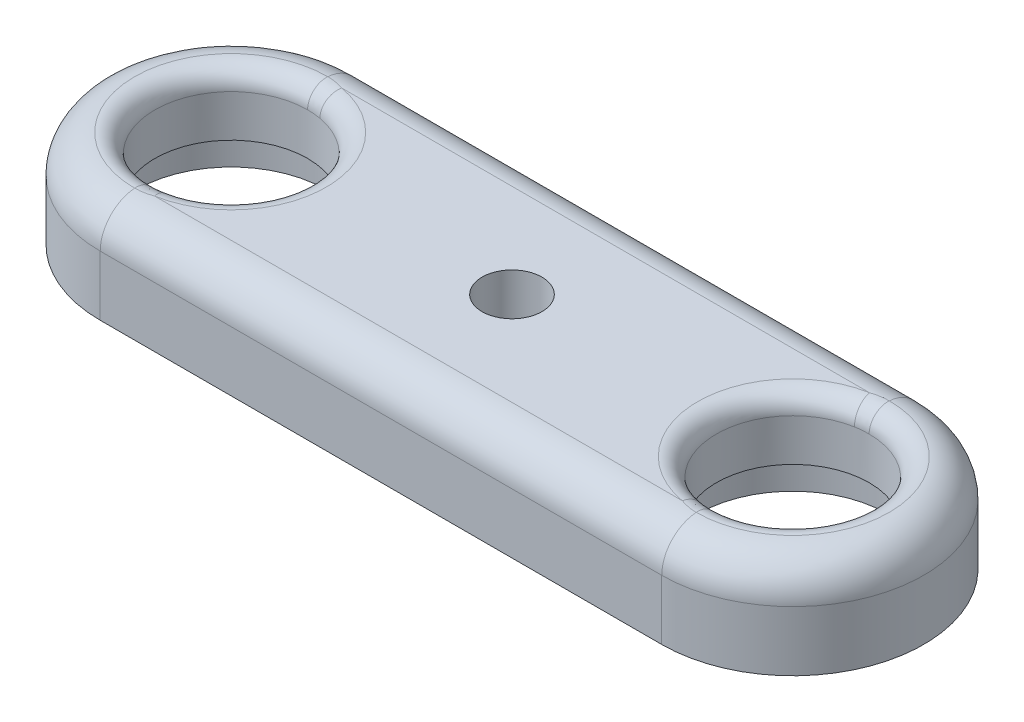
SolidWorks part; units mm, degrees
material "6061 Alloy"
ref_plane "Front Plane" through (0, 0, 0) normal (0, 0, 1) x (1, 0, 0)
ref_plane "Top Plane" through (0, 0, 0) normal (0, 1, 0) x (1, 0, 0)
ref_plane "Right Plane" through (0, 0, 0) normal (1, 0, 0) x (0, 0, -1)
sketch "Sketch1" plane through (0, 0, 0) normal (0, 1, 0) x (1, 0, 0)
  line L0 (-15, 0) -> (15, 0) construction
  line L1 (-15, 7) -> (15, 7)
  line L2 (-15, -7) -> (15, -7)
  arc A0 (-15, 7) -> (-15, -7) centre (-15, 0) ccw
  arc A1 (15, -7) -> (15, 7) centre (15, 0) ccw
  circle A2 centre (-15, 0) radius 4.08
  circle A3 centre (15, 0) radius 4.08
  point P3 (0, 0)
  dimension "D2" = 8.16
  dimension "D3" = 8.16
  dimension "D4" = 7
  dimension "D5" = 15
  dimension "D1" = 30
extrude "Boss-Extrude1" add sketch "Sketch1" along normal blind 5.2
sketch "Sketch2" plane through (0, 5.2, 0) normal (0, 1, 0) x (1, 0, 0)
  circle A3 centre (0, 0) radius 1.6
  dimension "D1" = 3.2
extrude "Cut-Extrude1" cut sketch "Sketch2" against normal blind 5.2
sketch "Sketch3" plane through (0, 0, 0) normal (0, -1, 0) x (1, 0, 0)
  circle A0 centre (-15, 0) radius 5.08
  circle A1 centre (15, 0) radius 5.08
  dimension "D1" = 10.16
  dimension "D2" = 10.16
extrude "Cut-Extrude2" cut sketch "Sketch3" against normal blind 1.95
fillet "Fillet1" radius 2 4 edges at (0, 5.2, 7) (-22, 5.2, 0) (0, 5.2, -7) (22, 5.2, 0)
fillet "Fillet2" radius 1 2 edges at (15, 5.2, 4.08) (-15, 5.2, 4.08)
